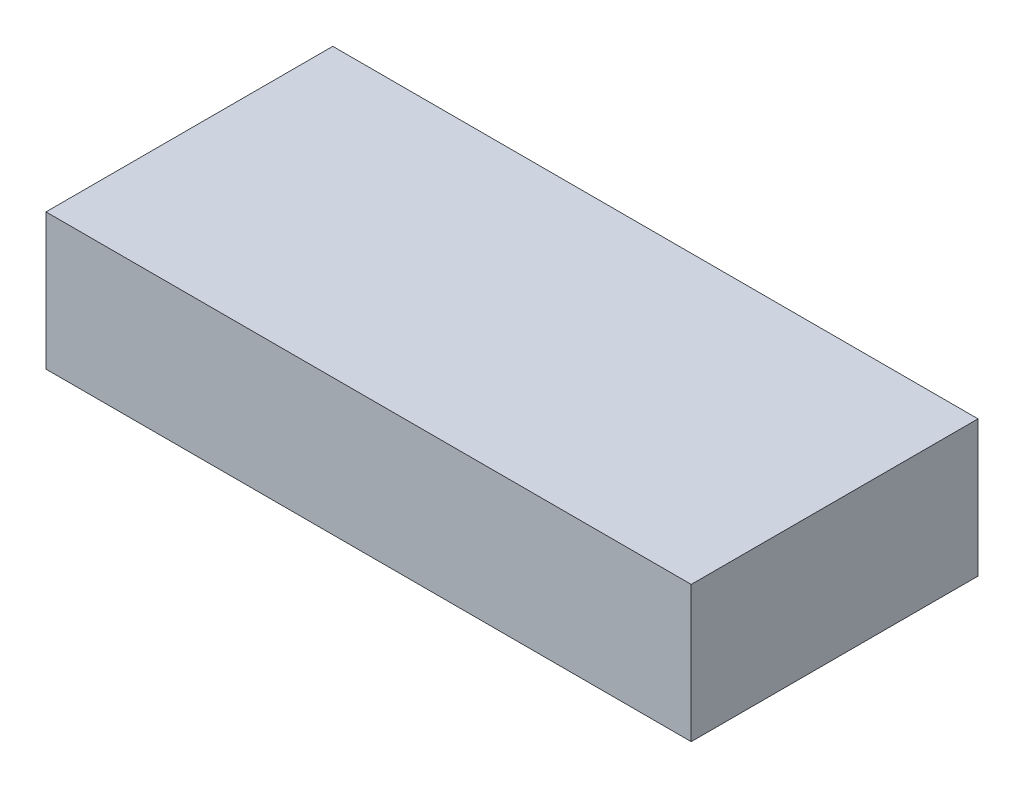
SolidWorks part; units mm, degrees
ref_plane "Front Plane" through (0, 0, 0) normal (0, 0, 1) x (1, 0, 0)
ref_plane "Top Plane" through (0, 0, 0) normal (0, 1, 0) x (1, 0, 0)
ref_plane "Right Plane" through (0, 0, 0) normal (1, 0, 0) x (0, 0, -1)
sketch "Sketch1" plane through (0, 0, 0) normal (0, 1, 0) x (1, 0, 0)
  line L1 (0, 0) -> (90, 0)
  line L2 (0, 0) -> (0, 40)
  line L3 (0, 40) -> (90, 40)
  line L4 (90, 0) -> (90, 40)
  dimension "D1" = 90
  dimension "D2" = 40
extrude "Boss-Extrude1" add sketch "Sketch1" along normal blind 19
